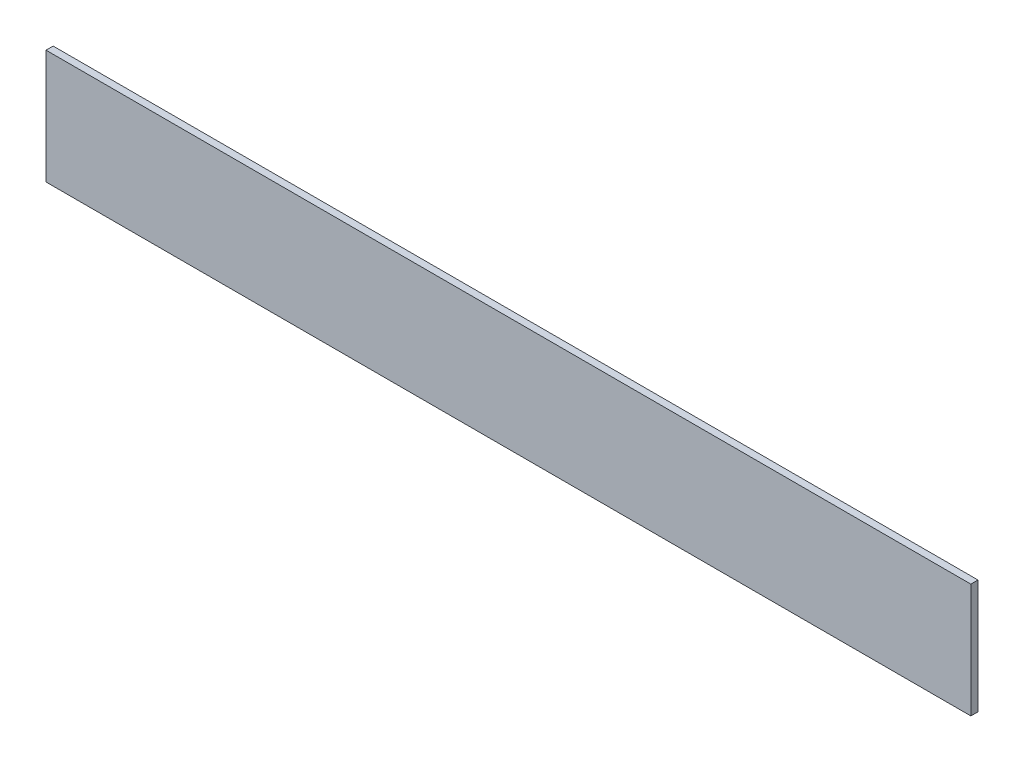
SolidWorks part; units mm, degrees
ref_plane "Front Plane" through (0, 0, 0) normal (0, 0, 1) x (1, 0, 0)
ref_plane "Top Plane" through (0, 0, 0) normal (0, 1, 0) x (1, 0, 0)
ref_plane "Right Plane" through (0, 0, 0) normal (1, 0, 0) x (0, 0, -1)
sketch "Sketch1" plane through (0, 0, 0) normal (0, 0, 1) x (1, 0, 0)
  line L1 (0, 0) -> (822.96, 0)
  line L2 (0, 0) -> (0, 101.6)
  line L3 (0, 101.6) -> (822.96, 101.6)
  line L4 (822.96, 0) -> (822.96, 101.6)
  line L7 (0, 0) -> (0, 101.6) construction
  line L8 (822.96, 0) -> (822.96, 101.6) construction
  dimension "D1" = 101.6
extrude "Boss-Extrude1" add sketch "Sketch1" along normal blind 6.35 contours L3 L4 L1 L2
